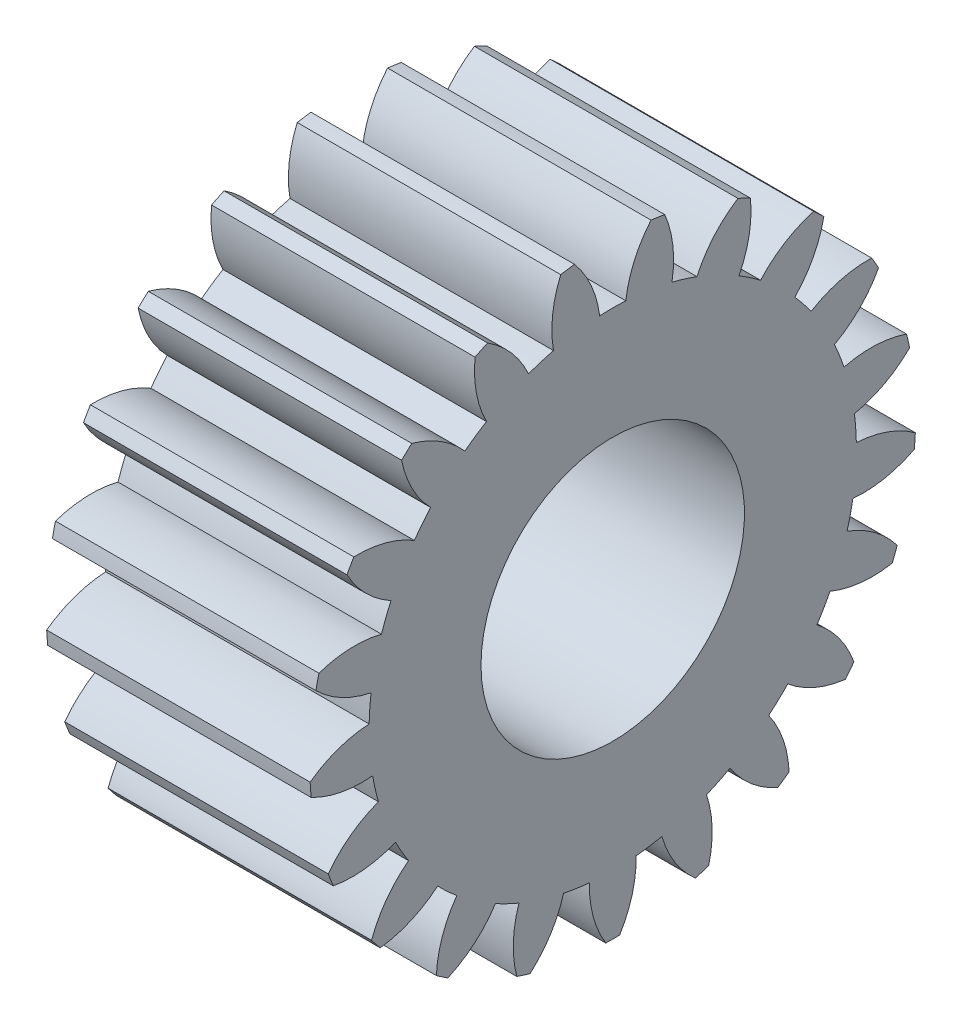
SolidWorks part; units mm, degrees
material "铬红铜，UNS C18200"
ref_plane "Plane1" through (0, 0, 0) normal (0, 0, 1) x (1, 0, 0)
ref_plane "Plane2" through (0, 0, 0) normal (0, 1, 0) x (1, 0, 0)
ref_plane "Plane3" through (0, 0, 0) normal (1, 0, 0) x (0, 0, -1)
sketch "HoldingSke" plane through (0, 0, 0) normal (0, 1, 0) x (1, 0, 0)
  line L0 (0, 0) -> (1.8672, -0.7167)
  line L1 (-15, 0) -> (100, 0) construction
  line L2 (0, 0) -> (-2.1039, 2.3779)
  line L3 (0, 0) -> (-11.863, 4.5341)
  line L4 (0, 0) -> (8.0624, 3.0949)
  line L5 (0, 0) -> (-9.3695, -3.4946)
  line L6 (0, 0) -> (-4.1448, -2.7965)
  line L7 (-2.1039, 2.3779) -> (0.0486, 12.1435)
  line L8 (-76.2, 54.61) -> (-75.3, 54.61)
  line L9 (-71.009, 38.7566) -> (-53.1078, 45.2721)
  line L10 (-76.2, 71.12) -> (104.1128, 71.12)
  line L11 (0, 0) -> (-5, 0)
  line L12 (-76.2, 101.6) -> (-76.181, 101.6)
  line L13 (24.9733, 27.94) -> (52.9518, 28.4284)
  line L14 (24.9733, 27.94) -> (24.9743, 27.94)
  line L15 (24.9733, 27.94) -> (100.4006, 29.5858)
  line L16 (-63.627, -0.5) -> (-12.827, -0.5)
  circle A0 centre (0, 0) radius 2.5
  circle A1 centre (0, 0) radius 4.5
  circle A2 centre (0, 0) radius 4.5
  circle A3 centre (0, 0) radius 2.5
  dimension "MHD" = 9
  dimension "Hub_dia" = 9
  dimension "Bore" = 5
  dimension "MBD" = 5
  dimension "Num_teeth" = 21
  dimension "Pitch_radius" = 180.3128
  dimension "Pitch" = 2
  dimension "Width" = 5
  dimension "Overall_len" = 10
  dimension "Show_teeth" = 21
  dimension "Thickness" = 5
  dimension "OAL" = 10.0001
  dimension "T_dim" = 0.9
  dimension "Ap" = 20
  dimension "H" = 19.05
  dimension "Backlash" = 0.019
  dimension "Addendum_fac" = 1
  dimension "Dedendum_fac" = 1.25
  dimension "Clearance_fac" = 0.25
  dimension "Dedendum_add" = 0.001
  dimension "Module" = 0.5
sketch "BasProSke" plane through (0, 0, 0) normal (0, 1, 0) x (1, 0, 0)
  line L0 (-10, 0) -> (60, 0) construction
  line L1 (0, 0) -> (0, 5.75)
  line L2 (0, 0) -> (5, 0)
  line L3 (5, 0) -> (5, 5.75)
  line L4 (5, 5.75) -> (0, 5.75)
  dimension "Diameter" = 11.5
  dimension "Thickness" = 5
revolve "Base-Revolve" add sketch "BasProSke" angle 360 about L0
sketch "TooCutSke" plane through (0, 0, 0) normal (1, 0, 0) x (0, 0, -1)
  line L1 (0, 0) -> (0, 107) construction
  line L2 (0, 0) -> (-0.4256, 5.2327) construction
  line L3 (0, 0) -> (-1.5613, 10.3584) construction
  line L4 (-0.4256, 5.2327) -> (-0.7806, 5.1792) construction
  arc A0 (0.2476, 4.6174) -> (-0.2476, 4.6174) centre (0, 0) ccw
  arc A1 (0.7462, 5.727) -> (-0.7462, 5.727) centre (0, 0) ccw
  circle A2 centre (0, 0) radius 5.25 construction
  circle A3 centre (0, 0) radius 4.9334 construction
  arc A4 (-0.2476, 4.6174) -> (-0.7462, 5.727) centre (-2.3303, 4.3484) ccw
  arc A5 (0.7462, 5.727) -> (0.2476, 4.6174) centre (2.3303, 4.3484) ccw
  dimension "Root_dia" = 9.248
  dimension "Overcut_dia" = 11.5508
  dimension "Pitch_dia" = 10.5
  dimension "Base_dia" = 9.8668
  dimension "Flank_rad" = 2.1
  dimension "Half_ang" = 8.571
  dimension "Half_CT" = 0.3591
extrude "ToothCut" cut sketch "TooCutSke" along normal through all
fillet "Breaks" [suppressed] radius 0.01
fillet "RootFillets" [suppressed] radius 0.126
pattern_circular "TeethCuts" count 21 every 17.143 about axis through (-10, 0, 0) along (1, 0, 0) of "ToothCut", "RootFillets", "Breaks"
sketch "HubNeaOneSke" plane through (0, 0, 0) normal (-1, 0, 0) x (0, 0, 1)
  circle A0 centre (0, 0) radius 4.5
  dimension "Diameter" = 9
extrude "HubNearOne" [suppressed] add sketch "HubNeaOneSke" along normal blind 5.0001
sketch "HubNeaBotSke" plane through (0, 0, 0) normal (-1, 0, 0) x (0, 0, 1)
  circle A0 centre (0, 0) radius 4.5
  dimension "Diameter" = 9
extrude "HubNearBoth" [suppressed] add sketch "HubNeaBotSke" along normal blind 2.5
ref_plane "FarPln" through (5, 0, 0) normal (1, 0, 0) x (0, 0, -1)
sketch "HubFarSke" plane through (5, 0, 0) normal (1, 0, 0) x (0, 0, -1)
  circle A0 centre (0, 0) radius 4.5
  dimension "Diameter" = 9
extrude "HubFar" [suppressed] add sketch "HubFarSke" along normal blind 2.5
sketch "BorSke" plane through (0, 0, 0) normal (1, 0, 0) x (0, 0, -1)
  circle A0 centre (0, 0) radius 2.5
  dimension "Diameter" = 5
extrude "Bore" cut sketch "BorSke" along normal mid plane 20.0001
sketch "KeySke" plane through (0, 0, 0) normal (1, 0, 0) x (0, 0, -1)
  line L0 (-1, 0) -> (-1, 3.4)
  line L1 (-1, 3.4) -> (1, 3.4)
  line L2 (1, 3.4) -> (1, 0)
  line L3 (0, 0) -> (0, 34) construction
  line L4 (-1, 0) -> (1, 0)
  dimension "Offset" = 3.4
  dimension "Width" = 2
extrude "Keyway" [suppressed] cut sketch "KeySke" along normal mid plane 20.0001
pattern_circular "Keyway2" [suppressed] count 2 every 90 about axis through (-10, 0, 0) along (1, 0, 0)
equation "' \"Module@HoldingSke\" = 6.35"
equation "' \"Num_teeth@HoldingSke\" = 12"
equation "' \"Ap@HoldingSke\" =  20"
equation "' \"Width@HoldingSke\" = 0.5 * 25.4"
equation "' \"Hub_dia@HoldingSke\"= 1 * 25.4"
equation "' \"Overall_len@HoldingSke\" = 1.0 * 25.4"
equation "' \"Bore@HoldingSke\" = 0.75 * 25.4"
equation "' \"T_dim@HoldingSke\" = 0.1 * 25.4"
equation "' \"Width@KeySke\" = 0.25 * 25.4"
equation "' \"Show_teeth@HoldingSke\" = 13"
equation "' \"Backlash@HoldingSke\" = 0.009 * 25.4"
equation "' \"Addendum_fac@HoldingSke\" = 1.0"
equation "' \"Dedendum_fac@HoldingSke\" = 1.25"
equation "' \"Dedendum_add@HoldingSke\" = 0.00005 * 25.4"
equation "' \"Clearance_fac@HoldingSke\" = 0.25"
equation "\"Pitch@HoldingSke\" = 1 / \"Module@HoldingSke\""
equation "\"Overcut_dia@TooCutSke\" = (\"Num_teeth@HoldingSke\" + 2 * \"Addendum_fac@HoldingSke\") / \"Pitch@HoldingSke\" + 0.002 * 25.4"
equation "\"Pitch_dia@TooCutSke\" = \"Num_teeth@HoldingSke\" / \"Pitch@HoldingSke\""
equation "\"Base_dia@TooCutSke\" = \"Num_teeth@HoldingSke\" / \"Pitch@HoldingSke\" * cos((\"Ap@HoldingSke\"  * 3.14159265 / 180))"
equation "\"Root_dia@TooCutSke\" = (\"Num_teeth@HoldingSke\" + 2) / \"Pitch@HoldingSke\" - 2 * (\"Addendum_fac@HoldingSke\" + \"Dedendum_fac@HoldingSke\") / \"Pitch@HoldingSke\" - \"Dedendum_add@HoldingSke\" * 2"
equation "\"Half_ang@TooCutSke\" = 180 / \"Num_teeth@HoldingSke\""
equation "\"Half_CT@TooCutSke\" = \"Num_teeth@HoldingSke\" / \"Pitch@HoldingSke\" * sin((3.14159265 / 2 / \"Num_teeth@HoldingSke\")) / 2 - 7 * \"Backlash@HoldingSke\" / 4"
equation "\"Flank_rad@TooCutSke\" = \"Num_teeth@HoldingSke\" / \"Pitch@HoldingSke\" / 5"
equation "\"Radius@RootFillets\" = \"Clearance_fac@HoldingSke\" / \"Pitch@HoldingSke\" + \"Dedendum_add@HoldingSke\""
equation "\"Break_rad@Breaks\" = 0.02 / \"Pitch@HoldingSke\""
equation "\"Thickness@HoldingSke\" = \"Width@HoldingSke\""
equation "\"OAL@HoldingSke\" = \"Thickness@HoldingSke\""
equation "\"MHD@HoldingSke\" = (\"Num_teeth@HoldingSke\" + 2) / \"Pitch@HoldingSke\" - 2 * (\"Addendum_fac@HoldingSke\" + \"Dedendum_fac@HoldingSke\")  / \"Pitch@HoldingSke\" - \"Dedendum_add@HoldingSke\" * 2"
equation "\"MBD@HoldingSke\" = (\"Num_teeth@HoldingSke\" + 2) / \"Pitch@HoldingSke\" - 2 * (\"Addendum_fac@HoldingSke\" + \"Dedendum_fac@HoldingSke\")  / \"Pitch@HoldingSke\" - \"Dedendum_add@HoldingSke\" * 2 - 0.002 * 25.4"
equation "\"MHD@HoldingSke\" = ((sgn( \"MHD@HoldingSke\" - \"Hub_dia@HoldingSke\" )-1)*( \"MHD@HoldingSke\" - \"Hub_dia@HoldingSke\" ))/-2+ \"Hub_dia@HoldingSke\""
equation "\"MBD@HoldingSke\" = ((sgn( \"MBD@HoldingSke\" - \"Bore@HoldingSke\" )-1)*( \"MBD@HoldingSke\" - \"Bore@HoldingSke\" ))/-2+ \"Bore@HoldingSke\""
equation "\"OAL@HoldingSke\" = ((sgn( \"OAL@HoldingSke\" - \"Overall_len@HoldingSke\" )+1)*( \"OAL@HoldingSke\" - \"Overall_len@HoldingSke\" ))/2 + \"Overall_len@HoldingSke\" + 0.000002 * 25.4"
equation "\"Num_teeth@TeethCuts\" = int( \"Show_teeth@HoldingSke\" ) + 1"
equation "\"Num_teeth@TeethCuts\" = ((sgn( \"Num_teeth@TeethCuts\" - \"Num_teeth@HoldingSke\" )-1)*( \"Num_teeth@TeethCuts\" - \"Num_teeth@HoldingSke\" ))/-2+ \"Num_teeth@HoldingSke\""
equation "\"Num_teeth@TeethCuts\" = ((sgn( \"Num_teeth@TeethCuts\" - 2.0)+1)*( \"Num_teeth@TeethCuts\" - 2.0))/2 +2.0"
equation "\"Angle@TeethCuts\" = 360.0 / \"Num_teeth@HoldingSke\""
equation "\"Diameter@BasProSke\" = (\"Num_teeth@HoldingSke\" + 2 * \"Addendum_fac@HoldingSke\") / \"Pitch@HoldingSke\""
equation "\"Thickness@BasProSke\"  = \"Thickness@HoldingSke\""
equation "' \"Fillet_rad@BasProSke\" =  \"Thickness@HoldingSke\" * 0.05"
equation "\"MHD@HoldingSke\" = ((sgn( \"MHD@HoldingSke\" - \"Root_dia@TooCutSke\" )-1)*( \"MHD@HoldingSke\" - \"Root_dia@TooCutSke\" ))/-2+ \"Root_dia@TooCutSke\""
equation "\"Diameter@HubNeaOneSke\" = \"MHD@HoldingSke\""
equation "\"Length@HubNearOne\" = \"OAL@HoldingSke\" - \"Thickness@BasProSke\""
equation "\"Diameter@HubNeaBotSke\" = \"MHD@HoldingSke\""
equation "\"Length@HubNearBoth\" = ( \"OAL@HoldingSke\" - \"Thickness@BasProSke\" ) / 2.0"
equation "\"Thickness@FarPln\" = \"Thickness@BasProSke\""
equation "\"Diameter@HubFarSke\" = \"MHD@HoldingSke\""
equation "\"Length@HubFar\" = ( \"OAL@HoldingSke\" - \"Thickness@BasProSke\" ) / 2.0"
equation "\"Diameter@BorSke\" = \"MBD@HoldingSke\""
equation "\"D1@Bore\" = \"OAL@HoldingSke\" * 2.0"
equation "\"D1@Keyway\" = \"OAL@HoldingSke\" * 2.0"
equation "\"Offset@KeySke\" = \"T_dim@HoldingSke\" + \"MBD@HoldingSke\" / 2.0"
